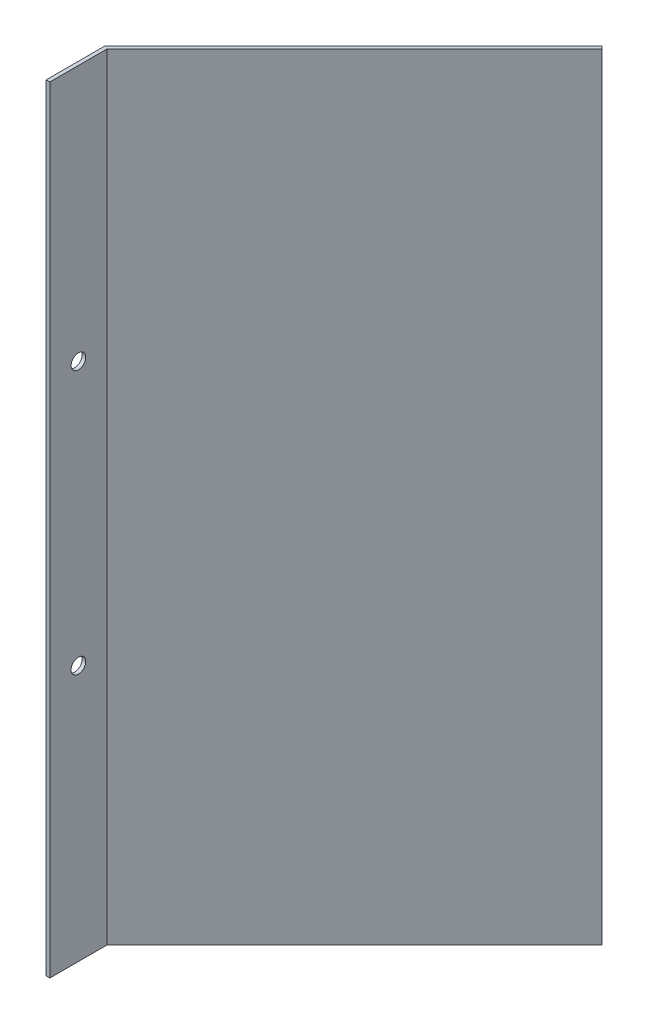
SolidWorks part; units mm, degrees
ref_plane "Front Plane" through (0, 0, 0) normal (0, 0, 1) x (1, 0, 0)
ref_plane "Top Plane" through (0, 0, 0) normal (0, 1, 0) x (1, 0, 0)
ref_plane "Right Plane" through (0, 0, 0) normal (1, 0, 0) x (0, 0, -1)
sketch "Sketch1" plane through (0, 0, 0) normal (0, 1, 0) x (1, 0, 0)
  line L0 (0, 0) -> (0, 50.8)
  line L1 (0, 50.8) -> (215.5261, 266.3261)
  line L2 (215.5261, 266.3261) -> (217.7712, 264.0811)
  line L3 (217.7712, 264.0811) -> (3.175, 49.4849)
  line L4 (3.175, 49.4849) -> (3.175, 0)
  line L5 (3.175, 0) -> (0, 0)
  dimension "D1" = 3.175
  dimension "D2" = 3.175
  dimension "D3" = 50.8
  dimension "D4" = 304.8
  dimension "D5" = 135
extrude "Boss-Extrude1" add sketch "Sketch1" along normal blind 673.1
sketch "Sketch2" plane through (3.175, 0, 0) normal (1, 0, 0) x (0, 0, -1)
  line L0 (24.7424, 673.1) -> (24.7424, 0) construction
  line L1 (0, 673.1) -> (49.4849, 673.1) construction
  line L2 (0, 0) -> (49.4849, 0) construction
  circle A0 centre (24.7424, 450.85) radius 6.35
  circle A1 centre (24.7424, 222.25) radius 6.35
  dimension "D1" = 222.25
  dimension "D2" = 450.85
extrude "Cut-Extrude1" cut sketch "Sketch2" against normal through all
